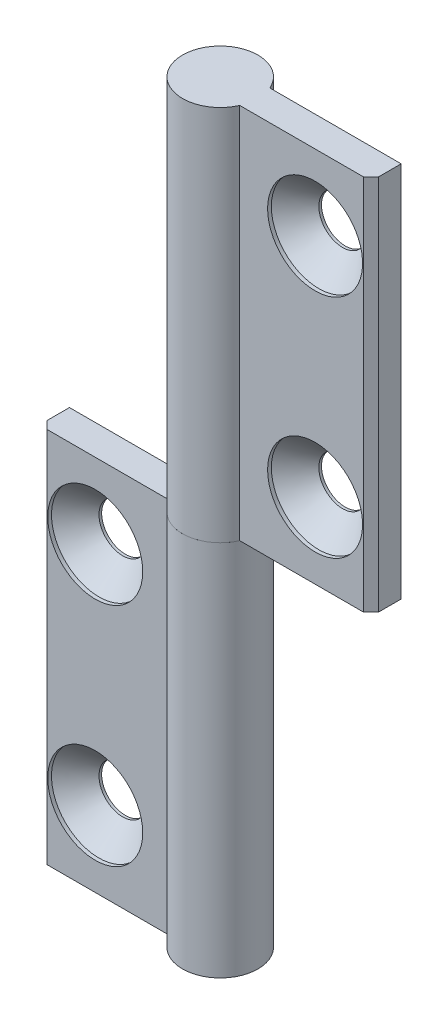
SolidWorks part; units mm, degrees
material "Алюминиевый сплав"
ref_plane "Спереди" through (0, 0, 0) normal (0, 0, 1) x (1, 0, 0)
ref_plane "Сверху" through (0, 0, 0) normal (0, 1, 0) x (1, 0, 0)
ref_plane "Справа" through (0, 0, 0) normal (1, 0, 0) x (0, 0, -1)
sketch "Эскиз1" plane through (0, 0, 0) normal (0, 1, 0) x (1, 0, 0)
  line L0 (-4.5826, 2) -> (-22, 2)
  line L1 (-22, 2) -> (-22, -1)
  line L2 (-22, -1) -> (-21, -2)
  line L3 (-21, -2) -> (-4.5826, -2)
  line L5 (-13.2913, 2) -> (-13.2913, -2) construction
  arc A0 (-4.5826, -2) -> (-4.5826, 2) centre (0, 0) ccw
  point P1 (-13.2913, 0)
  dimension "D5" = 5
  dimension "D1" = 17
  dimension "D2" = 4
  dimension "D3" = 3
  dimension "D4" = 45
extrude "Бобышка-Вытянуть1" add sketch "Эскиз1" along normal mid plane 50
hole_wizard "Зенковка для винта с полупотайной головкой M61" positions "Эскиз4" profile "Эскиз6" countersink size "M6" standard "ISO" end condition through all
sketch "Эскиз4" plane through (0, 0, 2) normal (0, 0, 1) x (1, 0, 0)
  line L0 (-14.5826, 15) -> (-14.5826, -15)
  line L2 (0.2087, -18.4577) -> (0.2087, 25) construction
  line L4 (5, 25) -> (-4.5826, 25) construction
  line L5 (-4.5826, 25) -> (-4.5826, -25) construction
  point P0 (-14.5826, 15)
  point P2 (-14.5826, -15)
  point P9 (-14.5826, 0)
  dimension "D1" = 30
  dimension "D2" = 10
sketch "Эскиз6" plane through (-14.5826, 15, 2) normal (1, 0, 0) x (0, -1, 0)
  line L0 (0, 0) -> (0, 7)
  line L1 (0, 7) -> (3.15, 7)
  line L2 (3.15, 7) -> (3.15, 3.65)
  line L3 (3.15, 3.65) -> (6.3, 0.5)
  line L4 (6.3, 0.5) -> (6.3, 0)
  line L6 (6.3, 0) -> (0, 0)
  line L7 (-3.15, 3.65) -> (-6.3, 0.5) construction
  line L11 (0, -6.35) -> (0, 107.95) construction
  dimension "Диаметр сквозного отверстия" = 6.3
  dimension "Глубина сквозного отверстия" = 7
  dimension "Диаметр зенковки" = 12.6
  dimension "Угол зенковки" = 90
  dimension "Утопленность" = 0.5
sketch "Угол раскрытия" plane through (0, 25, 0) normal (0, 1, 0) x (1, 0, 0)
  line L0 (0, 0) -> (0, -10)
  line L7 (-4.5826, 2) -> (-22, 2) construction
  dimension "D1" = 10
  dimension "D2" = 90
pattern_circular "Круговой массив1" count 2 over 360 about axis through (0, 25, 0) along (0, 0, 1) of bodies 106
